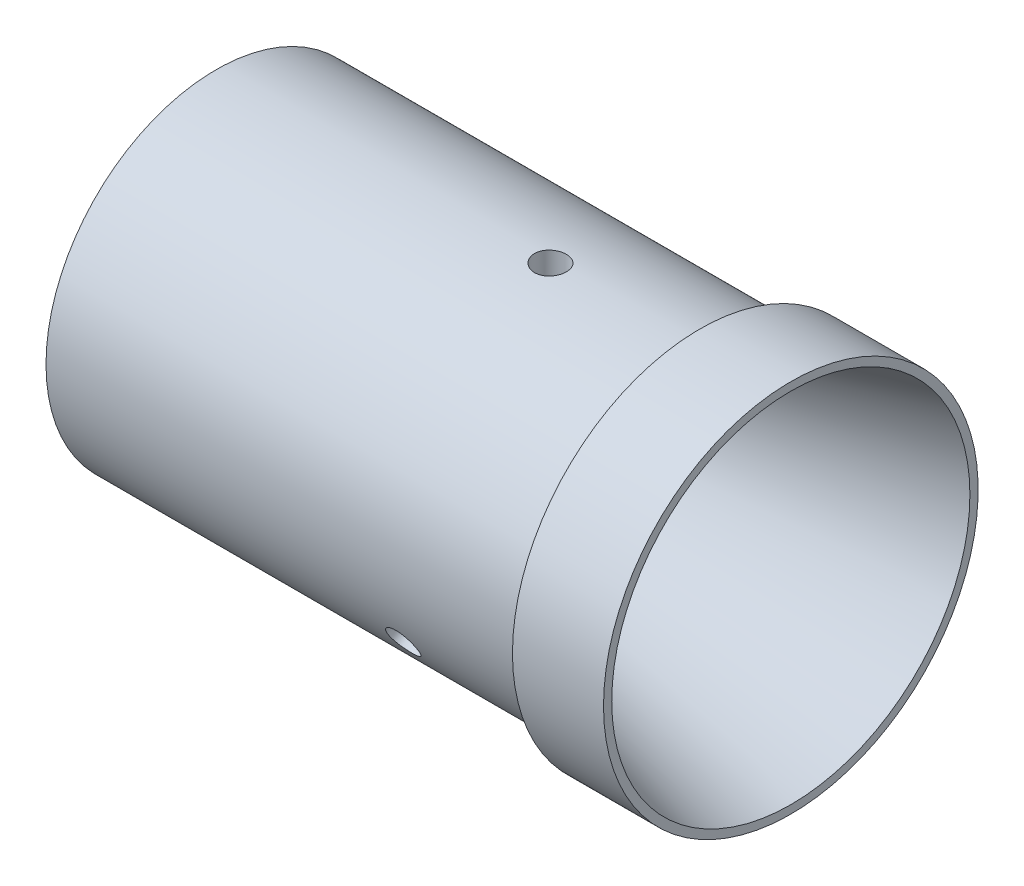
SolidWorks part; units mm, degrees
material "6061-T6 (SS)"
ref_plane "Front Plane" through (0, 0, 0) normal (0, 0, 1) x (1, 0, 0)
ref_plane "Top Plane" through (0, 0, 0) normal (0, 1, 0) x (1, 0, 0)
ref_plane "Right Plane" through (0, 0, 0) normal (1, 0, 0) x (0, 0, -1)
sketch "Sketch1" plane through (0, 0, 0) normal (0, 0, 1) x (1, 0, 0)
  line L0 (0, 14.478) -> (41.148, 14.478)
  line L1 (41.148, 14.478) -> (41.148, 15.9385)
  line L2 (41.148, 15.9385) -> (48.895, 15.9385)
  line L3 (48.895, 15.9385) -> (48.895, 15.2372)
  line L4 (48.895, 15.2372) -> (24.638, 8.7376)
  line L5 (24.638, 8.7376) -> (24.638, 10.3251)
  line L6 (0, 0) -> (87.5674, 0) construction
  line L7 (24.638, 8.7376) -> (48.895, 8.7376) construction
  line L8 (24.638, 10.3251) -> (7.62, 10.3251)
  line L9 (7.62, 10.3251) -> (7.62, 11.1633)
  line L10 (7.62, 11.1633) -> (5.842, 11.1633)
  line L11 (5.842, 11.1633) -> (5.842, 12.7)
  line L13 (5.842, 12.7) -> (0, 12.7)
  line L14 (0, 12.7) -> (0, 14.478)
  dimension "D1" = 14.478
  dimension "D2" = 15.9385
  dimension "D3" = 17.018
  dimension "D4" = 8.7376
  dimension "D5" = 15
  dimension "D6" = 48.895
  dimension "D7" = 10.3251
  dimension "D8" = 11.1633
  dimension "D9" = 1.778
  dimension "D10" = 12.7
  dimension "D11" = 5.842
  dimension "D12" = 16.51
revolve "Revolve1" add sketch "Sketch1" angle 360 about L6
ref_plane "Plane1" through (0, 14.478, 0) normal (0, 1, 0) x (1, 0, 0)
hole_wizard "#6-32 Tapped Hole1" positions "Sketch2" profile "Sketch3" tap size "#6-32" standard "ANSI Inch"
sketch "Sketch2" plane through (0, 14.478, 0) normal (0, 1, 0) x (1, 0, 0)
  line L0 (41.148, 15.9385) -> (41.148, -15.9385) construction
  point P0 (28.448, 0)
  dimension "D1" = 12.7
sketch "Sketch3" plane through (28.448, 14.478, 0) normal (1, 0, 0) x (0, 0, 1)
  line L0 (0, 0) -> (0, 3.175)
  line L1 (0, 3.175) -> (1.3525, 2.3623)
  line L2 (1.3525, 2.3623) -> (1.3525, 0)
  line L5 (1.3525, 0) -> (0, 0)
  line L10 (0, 3.175) -> (-1.3526, 2.3623) construction
  line L11 (0, -6.35) -> (0, 107.95) construction
  dimension "Tap Drill Dia." = 2.7051
  dimension "Tap Drill Depth" = 3.175
  dimension "Drill Angle" = 118
cosmetic thread "Hole Thread1" parameters "D1"=7.0104, "D2"=3.5052
pattern_circular "CirPattern1" count 3 over 360 about axis through (0, 0, 0) along (-1, 0, 0) of "#6-32 Tapped Hole1"
cosmetic thread "Hole Thread2" parameters "D1"=7.0104, "D2"=3.5052
cosmetic thread "Hole Thread3" parameters "D1"=7.0104, "D2"=3.5052
